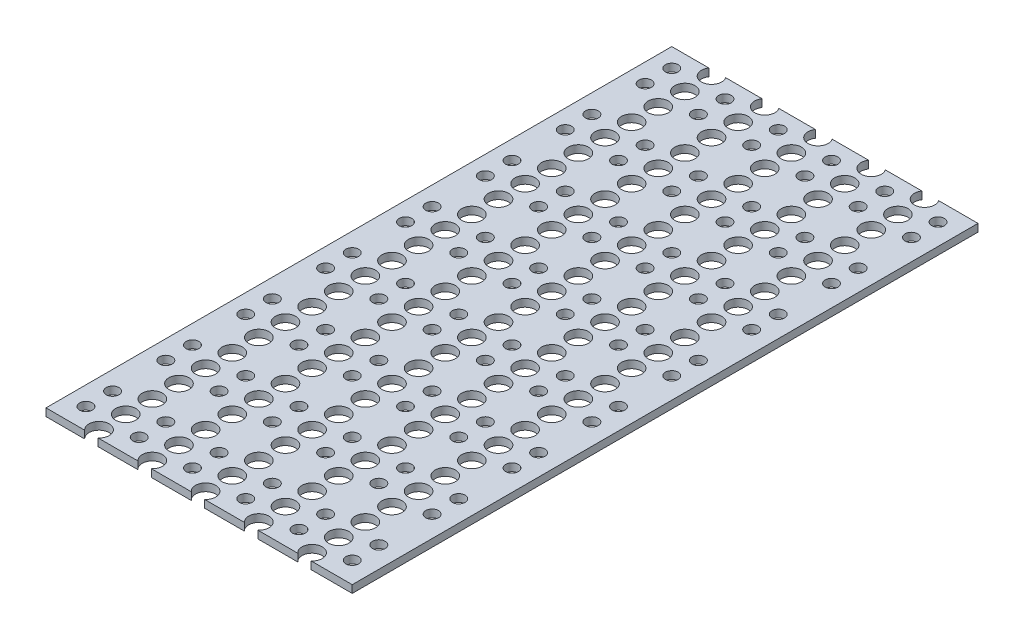
SolidWorks part; units mm, degrees
ref_plane "Front" through (0, 0, 0) normal (0, 0, 1) x (1, 0, 0)
ref_plane "Top" through (0, 0, 0) normal (0, 1, 0) x (1, 0, 0)
ref_plane "Right" through (0, 0, 0) normal (1, 0, 0) x (0, 0, -1)
sketch "Sketch1" plane through (0, 0, 0) normal (0, 1, 0) x (1, 0, 0)
  line L1 (-120.75, -246.75) -> (120.75, -246.75)
  line L2 (-120.75, -246.75) -> (-120.75, 246.75)
  line L3 (-120.75, 246.75) -> (120.75, 246.75)
  line L4 (120.75, -246.75) -> (120.75, 246.75)
  line L5 (-120.75, -246.75) -> (120.75, 246.75) construction
  line L6 (-120.75, 246.75) -> (120.75, -246.75) construction
  point P0 (0, 0)
  dimension "D1" = 241.5
  dimension "D2" = 493.5
extrude "Boss-Extrude1" add sketch "Sketch1" along normal blind 6
sketch "Sketch2" plane through (0, 6, 0) normal (0, 1, 0) x (1, 0, 0)
  line L0 (120.75, 246.75) -> (-120.75, 246.75) construction
  line L2 (-120.75, 246.75) -> (-120.75, -246.75) construction
  circle A0 centre (-105.9, 231.895) radius 5
  circle A1 centre (-63.9, 231.895) radius 5
  circle A2 centre (-21.9, 231.895) radius 5
  circle A3 centre (20.1, 231.895) radius 5
  circle A4 centre (62.1, 231.895) radius 5
  circle A5 centre (-105.9, 210.895) radius 5
  circle A6 centre (-63.9, 210.895) radius 5
  circle A7 centre (-21.9, 210.895) radius 5
  circle A8 centre (20.1, 210.895) radius 5
  circle A9 centre (62.1, 210.895) radius 5
  circle A15 centre (-105.9, 168.895) radius 5
  circle A16 centre (-63.9, 168.895) radius 5
  circle A17 centre (-21.9, 168.895) radius 5
  circle A18 centre (20.1, 168.895) radius 5
  circle A19 centre (62.1, 168.895) radius 5
  circle A20 centre (-105.9, 147.895) radius 5
  circle A21 centre (-63.9, 147.895) radius 5
  circle A22 centre (-21.9, 147.895) radius 5
  circle A23 centre (20.1, 147.895) radius 5
  circle A24 centre (62.1, 147.895) radius 5
  circle A30 centre (-105.9, 105.895) radius 5
  circle A31 centre (-63.9, 105.895) radius 5
  circle A32 centre (-21.9, 105.895) radius 5
  circle A33 centre (20.1, 105.895) radius 5
  circle A34 centre (62.1, 105.895) radius 5
  circle A35 centre (-105.9, 84.895) radius 5
  circle A36 centre (-63.9, 84.895) radius 5
  circle A37 centre (-21.9, 84.895) radius 5
  circle A38 centre (20.1, 84.895) radius 5
  circle A39 centre (62.1, 84.895) radius 5
  circle A45 centre (-105.9, 42.895) radius 5
  circle A46 centre (-63.9, 42.895) radius 5
  circle A47 centre (-21.9, 42.895) radius 5
  circle A48 centre (20.1, 42.895) radius 5
  circle A49 centre (62.1, 42.895) radius 5
  circle A50 centre (-105.9, 21.895) radius 5
  circle A51 centre (-63.9, 21.895) radius 5
  circle A52 centre (-21.9, 21.895) radius 5
  circle A53 centre (20.1, 21.895) radius 5
  circle A54 centre (62.1, 21.895) radius 5
  circle A60 centre (104.1, 231.895) radius 5
  circle A61 centre (104.1, 210.895) radius 5
  circle A63 centre (104.1, 168.895) radius 5
  circle A64 centre (104.1, 147.895) radius 5
  circle A66 centre (104.1, 105.895) radius 5
  circle A67 centre (104.1, 84.895) radius 5
  circle A69 centre (104.1, 42.895) radius 5
  circle A70 centre (104.1, 21.895) radius 5
  circle A72 centre (-105.9, -20.105) radius 5
  circle A73 centre (-63.9, -20.105) radius 5
  circle A74 centre (-21.9, -20.105) radius 5
  circle A75 centre (20.1, -20.105) radius 5
  circle A76 centre (62.1, -20.105) radius 5
  circle A77 centre (104.1, -20.105) radius 5
  circle A78 centre (-105.9, -41.105) radius 5
  circle A79 centre (-63.9, -41.105) radius 5
  circle A80 centre (-21.9, -41.105) radius 5
  circle A81 centre (20.1, -41.105) radius 5
  circle A82 centre (62.1, -41.105) radius 5
  circle A83 centre (104.1, -41.105) radius 5
  circle A90 centre (-105.9, -83.105) radius 5
  circle A91 centre (-63.9, -83.105) radius 5
  circle A92 centre (-21.9, -83.105) radius 5
  circle A93 centre (20.1, -83.105) radius 5
  circle A94 centre (62.1, -83.105) radius 5
  circle A95 centre (104.1, -83.105) radius 5
  circle A96 centre (-105.9, -104.105) radius 5
  circle A97 centre (-63.9, -104.105) radius 5
  circle A98 centre (-21.9, -104.105) radius 5
  circle A99 centre (20.1, -104.105) radius 5
  circle A100 centre (62.1, -104.105) radius 5
  circle A101 centre (104.1, -104.105) radius 5
  circle A108 centre (-105.9, -146.105) radius 5
  circle A109 centre (-63.9, -146.105) radius 5
  circle A110 centre (-21.9, -146.105) radius 5
  circle A111 centre (20.1, -146.105) radius 5
  circle A112 centre (62.1, -146.105) radius 5
  circle A113 centre (104.1, -146.105) radius 5
  circle A114 centre (-105.9, -167.105) radius 5
  circle A115 centre (-63.9, -167.105) radius 5
  circle A116 centre (-21.9, -167.105) radius 5
  circle A117 centre (20.1, -167.105) radius 5
  circle A118 centre (62.1, -167.105) radius 5
  circle A119 centre (104.1, -167.105) radius 5
  circle A126 centre (-105.9, -209.105) radius 5
  circle A127 centre (-63.9, -209.105) radius 5
  circle A128 centre (-21.9, -209.105) radius 5
  circle A129 centre (20.1, -209.105) radius 5
  circle A130 centre (62.1, -209.105) radius 5
  circle A131 centre (104.1, -209.105) radius 5
  circle A132 centre (-105.9, -230.105) radius 5
  circle A133 centre (-63.9, -230.105) radius 5
  circle A134 centre (-21.9, -230.105) radius 5
  circle A135 centre (20.1, -230.105) radius 5
  circle A136 centre (62.1, -230.105) radius 5
  circle A137 centre (104.1, -230.105) radius 5
  circle A138 centre (-63.9, 189.895) radius 5 [skipped]
  circle A139 centre (-21.9, 189.895) radius 5 [skipped]
  circle A140 centre (20.1, 189.895) radius 5 [skipped]
  circle A141 centre (62.1, 189.895) radius 5 [skipped]
  circle A142 centre (104.1, 189.895) radius 5 [skipped]
  circle A143 centre (-63.9, 126.895) radius 5 [skipped]
  circle A144 centre (-21.9, 126.895) radius 5 [skipped]
  circle A145 centre (20.1, 126.895) radius 5 [skipped]
  circle A146 centre (62.1, 126.895) radius 5 [skipped]
  circle A147 centre (104.1, 126.895) radius 5 [skipped]
  circle A148 centre (-63.9, 63.895) radius 5 [skipped]
  circle A149 centre (-21.9, 63.895) radius 5 [skipped]
  circle A150 centre (20.1, 63.895) radius 5 [skipped]
  circle A151 centre (62.1, 63.895) radius 5 [skipped]
  circle A152 centre (104.1, 63.895) radius 5 [skipped]
  circle A153 centre (-105.9, 189.895) radius 5 [skipped]
  circle A154 centre (-105.9, 126.895) radius 5 [skipped]
  circle A155 centre (-105.9, 63.895) radius 5 [skipped]
  circle A156 centre (-63.9, 0.895) radius 5 [skipped]
  circle A157 centre (-21.9, 0.895) radius 5 [skipped]
  circle A158 centre (20.1, 0.895) radius 5 [skipped]
  circle A159 centre (62.1, 0.895) radius 5 [skipped]
  circle A160 centre (104.1, 0.895) radius 5 [skipped]
  circle A161 centre (-63.9, -62.105) radius 5 [skipped]
  circle A162 centre (-21.9, -62.105) radius 5 [skipped]
  circle A163 centre (20.1, -62.105) radius 5 [skipped]
  circle A164 centre (62.1, -62.105) radius 5 [skipped]
  circle A165 centre (104.1, -62.105) radius 5 [skipped]
  circle A166 centre (-63.9, -125.105) radius 5 [skipped]
  circle A167 centre (20.1, -125.105) radius 5 [skipped]
  circle A168 centre (62.1, -125.105) radius 5 [skipped]
  circle A169 centre (104.1, -125.105) radius 5 [skipped]
  circle A170 centre (-105.9, 0.895) radius 5 [skipped]
  circle A171 centre (-105.9, -62.105) radius 5 [skipped]
  circle A172 centre (-105.9, -125.105) radius 5 [skipped]
  circle A173 centre (-21.9, -125.105) radius 5 [skipped]
  circle A174 centre (-21.9, -188.105) radius 5 [skipped]
  circle A175 centre (20.1, -188.105) radius 5 [skipped]
  circle A176 centre (62.1, -188.105) radius 5 [skipped]
  circle A177 centre (104.1, -188.105) radius 5 [skipped]
  circle A178 centre (-105.9, -188.105) radius 5 [skipped]
  circle A179 centre (-63.9, -188.105) radius 5 [skipped]
  dimension "D3" = 10
  dimension "D1" = 14.855
  dimension "D2" = 14.85
  dimension "D4" = 6
  dimension "D5" = 23
extrude "Cut-Extrude1" cut sketch "Sketch2" against normal through all
sketch "Sketch3" plane through (0, 6, 0) normal (0, 1, 0) x (1, 0, 0)
  line L0 (-120.75, 246.75) -> (-120.75, -246.75) construction
  line L1 (120.75, 246.75) -> (-120.75, 246.75) construction
  circle A0 centre (-84.9, 242.25) radius 8
  circle A1 centre (-42.9, 242.25) radius 8
  circle A2 centre (-0.9, 242.25) radius 8
  circle A3 centre (41.1, 242.25) radius 8
  circle A4 centre (83.1, 242.25) radius 8
  circle A5 centre (-42.9, 221.25) radius 8
  circle A6 centre (-0.9, 221.25) radius 8
  circle A7 centre (41.1, 221.25) radius 8
  circle A8 centre (83.1, 221.25) radius 8
  circle A9 centre (-42.9, 200.25) radius 8
  circle A10 centre (-0.9, 200.25) radius 8
  circle A11 centre (41.1, 200.25) radius 8
  circle A12 centre (83.1, 200.25) radius 8
  circle A13 centre (-42.9, 179.25) radius 8
  circle A14 centre (-0.9, 179.25) radius 8
  circle A15 centre (41.1, 179.25) radius 8
  circle A16 centre (83.1, 179.25) radius 8
  circle A17 centre (-42.9, 158.25) radius 8
  circle A18 centre (-0.9, 158.25) radius 8
  circle A19 centre (41.1, 158.25) radius 8
  circle A20 centre (83.1, 158.25) radius 8
  circle A21 centre (-42.9, 137.25) radius 8
  circle A22 centre (-0.9, 137.25) radius 8
  circle A23 centre (41.1, 137.25) radius 8
  circle A24 centre (83.1, 137.25) radius 8
  circle A25 centre (-42.9, 116.25) radius 8
  circle A26 centre (-0.9, 116.25) radius 8
  circle A27 centre (41.1, 116.25) radius 8
  circle A28 centre (83.1, 116.25) radius 8
  circle A29 centre (-42.9, 95.25) radius 8
  circle A30 centre (-0.9, 95.25) radius 8
  circle A31 centre (41.1, 95.25) radius 8
  circle A32 centre (83.1, 95.25) radius 8
  circle A33 centre (-42.9, 74.25) radius 8
  circle A34 centre (-0.9, 74.25) radius 8
  circle A35 centre (41.1, 74.25) radius 8
  circle A36 centre (83.1, 74.25) radius 8
  circle A37 centre (-42.9, 53.25) radius 8
  circle A38 centre (-0.9, 53.25) radius 8
  circle A39 centre (41.1, 53.25) radius 8
  circle A40 centre (83.1, 53.25) radius 8
  circle A41 centre (-42.9, 32.25) radius 8
  circle A42 centre (-0.9, 32.25) radius 8
  circle A43 centre (41.1, 32.25) radius 8
  circle A44 centre (83.1, 32.25) radius 8
  circle A45 centre (-42.9, 11.25) radius 8
  circle A46 centre (-0.9, 11.25) radius 8
  circle A47 centre (41.1, 11.25) radius 8
  circle A48 centre (83.1, 11.25) radius 8
  circle A49 centre (-42.9, -9.75) radius 8
  circle A50 centre (-0.9, -9.75) radius 8
  circle A51 centre (41.1, -9.75) radius 8
  circle A52 centre (83.1, -9.75) radius 8
  circle A53 centre (-42.9, -30.75) radius 8
  circle A54 centre (-0.9, -30.75) radius 8
  circle A55 centre (41.1, -30.75) radius 8
  circle A56 centre (83.1, -30.75) radius 8
  circle A57 centre (-42.9, -51.75) radius 8
  circle A58 centre (-0.9, -51.75) radius 8
  circle A59 centre (41.1, -51.75) radius 8
  circle A60 centre (83.1, -51.75) radius 8
  circle A61 centre (-42.9, -72.75) radius 8
  circle A62 centre (-0.9, -72.75) radius 8
  circle A63 centre (41.1, -72.75) radius 8
  circle A64 centre (83.1, -72.75) radius 8
  circle A65 centre (-42.9, -93.75) radius 8
  circle A66 centre (-0.9, -93.75) radius 8
  circle A67 centre (41.1, -93.75) radius 8
  circle A68 centre (83.1, -93.75) radius 8
  circle A69 centre (-42.9, -114.75) radius 8
  circle A70 centre (-0.9, -114.75) radius 8
  circle A71 centre (41.1, -114.75) radius 8
  circle A72 centre (83.1, -114.75) radius 8
  circle A73 centre (-42.9, -135.75) radius 8
  circle A74 centre (-0.9, -135.75) radius 8
  circle A75 centre (41.1, -135.75) radius 8
  circle A76 centre (83.1, -135.75) radius 8
  circle A77 centre (-42.9, -156.75) radius 8
  circle A78 centre (-0.9, -156.75) radius 8
  circle A79 centre (41.1, -156.75) radius 8
  circle A80 centre (83.1, -156.75) radius 8
  circle A81 centre (-42.9, -177.75) radius 8
  circle A82 centre (-0.9, -177.75) radius 8
  circle A83 centre (41.1, -177.75) radius 8
  circle A84 centre (83.1, -177.75) radius 8
  circle A85 centre (-42.9, -198.75) radius 8
  circle A86 centre (-0.9, -198.75) radius 8
  circle A87 centre (41.1, -198.75) radius 8
  circle A88 centre (83.1, -198.75) radius 8
  circle A89 centre (-42.9, -219.75) radius 8
  circle A90 centre (-0.9, -219.75) radius 8
  circle A91 centre (41.1, -219.75) radius 8
  circle A92 centre (83.1, -219.75) radius 8
  circle A93 centre (-42.9, -240.75) radius 8
  circle A94 centre (-0.9, -240.75) radius 8
  circle A95 centre (41.1, -240.75) radius 8
  circle A96 centre (83.1, -240.75) radius 8
  circle A97 centre (-84.9, 221.25) radius 8
  circle A98 centre (-84.9, 200.25) radius 8
  circle A99 centre (-84.9, 179.25) radius 8
  circle A100 centre (-84.9, 158.25) radius 8
  circle A101 centre (-84.9, 137.25) radius 8
  circle A102 centre (-84.9, 116.25) radius 8
  circle A103 centre (-84.9, 95.25) radius 8
  circle A104 centre (-84.9, 74.25) radius 8
  circle A105 centre (-84.9, 53.25) radius 8
  circle A106 centre (-84.9, 32.25) radius 8
  circle A107 centre (-84.9, 11.25) radius 8
  circle A108 centre (-84.9, -9.75) radius 8
  circle A109 centre (-84.9, -30.75) radius 8
  circle A110 centre (-84.9, -51.75) radius 8
  circle A111 centre (-84.9, -72.75) radius 8
  circle A112 centre (-84.9, -93.75) radius 8
  circle A113 centre (-84.9, -114.75) radius 8
  circle A114 centre (-84.9, -135.75) radius 8
  circle A115 centre (-84.9, -156.75) radius 8
  circle A116 centre (-84.9, -177.75) radius 8
  circle A117 centre (-84.9, -198.75) radius 8
  circle A118 centre (-84.9, -219.75) radius 8
  circle A119 centre (-84.9, -240.75) radius 8
  dimension "D1" = 16
  dimension "D2" = 35.85
  dimension "D3" = 4.5
  dimension "D4" = 5
  dimension "D5" = 24
extrude "Cut-Extrude2" cut sketch "Sketch3" against normal through all
sketch "Sketch4" plane through (0, 6, 0) normal (0, 1, 0) x (1, 0, 0)
  line L1 (-120.75, 246.75) -> (120.75, 246.75)
  line L2 (-120.75, 246.75) -> (-120.75, -246.75)
  line L3 (-120.75, -246.75) -> (120.75, -246.75)
  line L4 (120.75, 246.75) -> (120.75, -246.75)
extrude "Cut-Extrude3" [suppressed] cut sketch "Sketch4" against normal offset from surface (3 mm away) 3
